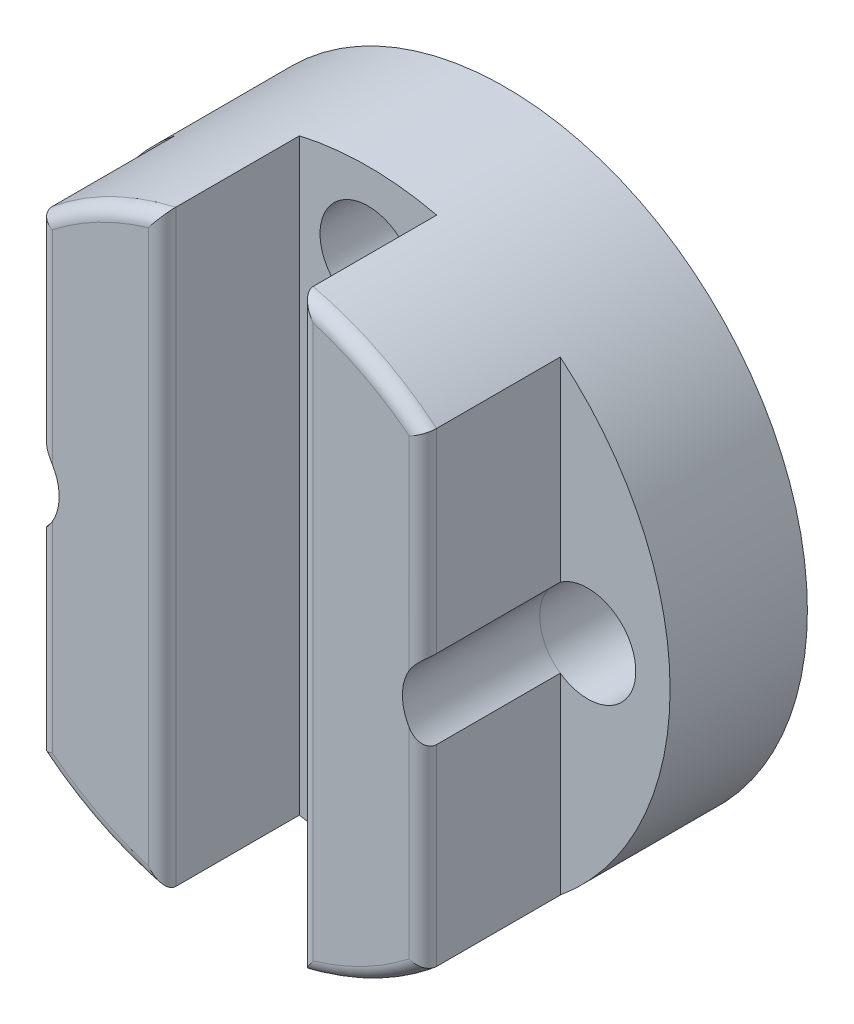
SolidWorks part; units mm, degrees
material "ABS PC"
ref_plane "Plan de face" through (0, 0, 0) normal (0, 0, 1) x (1, 0, 0)
ref_plane "Plan de dessus" through (0, 0, 0) normal (0, 1, 0) x (1, 0, 0)
ref_plane "Plan de droite" through (0, 0, 0) normal (1, 0, 0) x (0, 0, -1)
sketch "Esquisse1" plane through (0, 0, 0) normal (0, 0, 1) x (1, 0, 0)
  circle A0 centre (0, 0) radius 11
  dimension "D1" = 22
extrude "Boss.-Extru.1" add sketch "Esquisse1" along normal blind 5
sketch "Esquisse2" plane through (0, 0, 5) normal (0, 0, 1) x (1, 0, 0)
  line L0 (0, 5.7045) -> (0, -6.8994) construction
  line L1 (-7, 8.4853) -> (-7, -8.4853)
  line L2 (-2.5, 10.7121) -> (-2.5, -10.7121)
  line L3 (7, 8.4853) -> (7, -8.4853)
  line L4 (2.5, 10.7121) -> (2.5, -10.7121)
  circle A0 centre (0, 0) radius 11 construction
  arc A1 (-2.5, -10.7121) -> (2.5, -10.7121) centre (0, 0) ccw
  arc A2 (2.5, 10.7121) -> (-2.5, 10.7121) centre (0, 0) ccw
  circle A3 centre (0, 0) radius 11
  circle M1 centre (0, 0) radius 11
  dimension "D1" = 5
  dimension "D2" = 4.5
extrude "Boss.-Extru.3" add sketch "Esquisse2" along normal blind 5 contours L2 L1 M1 | L4 L3 M1
fillet "Congé3" radius 0.5 8 edges at (4.8788, 9.8589, 10) (4.8788, -9.8589, 10) (7, 0, 10) (2.5, 0, 10) (-4.8788, 9.8589, 10) (-4.8788, -9.8589, 10) (-2.5, 0, 10) (-7, 0, 10)
sketch3d "Esquisse3D1"
  circle A0 centre (0.0002, -8.0502, 0) radius 1.05
  circle A1 centre (8.0002, -0.0502, 0) radius 1.05
  circle A2 centre (0.0002, 7.9498, 0) radius 1.05
  circle A3 centre (-7.9998, -0.0502, 0) radius 1.05
  circle A4 centre (0, 0, 0) radius 11 construction
  point P2 (-7.9998, -0.0502, 1.05)
  point P5 (0.0002, 7.9498, 1.05)
  point P8 (8.0002, -0.0502, 1.05)
  point P11 (0.0002, -8.0502, 1.05)
  point P14 (0, 0, 11)
  point P15 (0, 0, 0)
  point P16 (0, 0, 0)
  dimension "D1" = 8
  dimension "D2" = 8
  dimension "D3" = 8
  dimension "D4" = 8
  dimension "D5" = 8
  dimension "D6" = 11.3137
  dimension "D7" = 8
extrude "Enlèv. mat.-Extru.1" cut sketch "Esquisse3D1" along direction (0, 0, 1) on the side against the normal through all
sketch3d "Esquisse3D2"
  circle A0 centre (-8, 0, 5) radius 1.75
  circle A1 centre (0.05, -8, 5) radius 1.75
  circle A2 centre (0, 8, 5) radius 1.75
  circle A3 centre (8, -0.0502, 5) radius 1.75
  point P0 (0, 0, 5)
  point P1 (0, 0, 5)
  point P4 (-8, 0, 6.75)
  point P7 (0.05, -8, 6.75)
  point P8 (0, 0, 5)
  point P11 (0, 8, 6.75)
  point P12 (0, 0, 5)
  point P15 (8, -0.0502, 6.75)
  point P16 (0, 0, 5)
  point P18 (0, 0, 5)
  dimension "D1" = 8
  dimension "D3" = 3.5
  dimension "D2" = 8
  dimension "D6" = 3.5
  dimension "D4" = 8
  dimension "D5" = 8
  dimension "D7" = 8
  dimension "D8" = 8
extrude "Enlèv. mat.-Extru.2" cut sketch "Esquisse3D2" along direction (0, 0, 1) on the side against the normal blind 2.5
ref_plane "Plan1" through (0, 0, 5) normal (0, 0, 1) x (1, 0, 0)
sketch "Esquisse4" plane through (0, 0, 5) normal (0, 0, 1) x (1, 0, 0)
  circle A0 centre (-7.9998, -0.0502) radius 1.75
  circle A3 centre (8.0002, -0.0502) radius 1.75
extrude "Enlèv. mat.-Extru.3" cut sketch "Esquisse4" along normal through all
